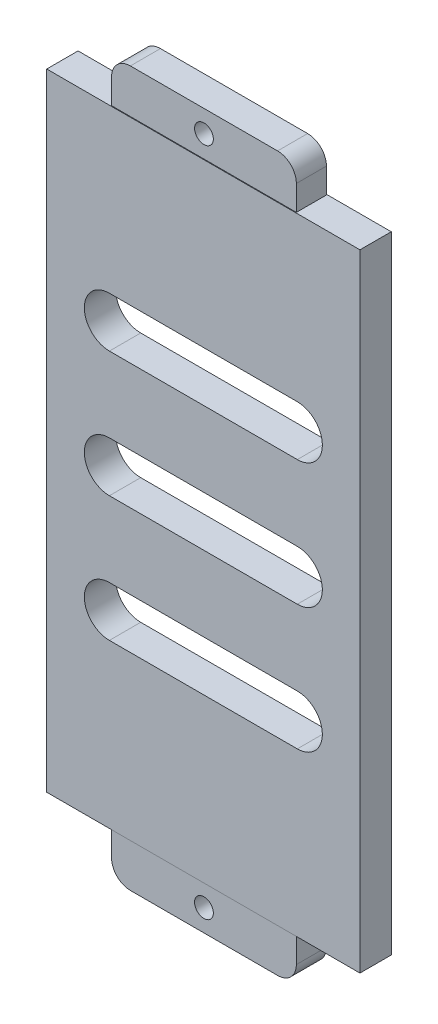
SolidWorks part; units mm, degrees
ref_plane "前视基准面" through (0, 0, 0) normal (0, 0, 1) x (1, 0, 0)
ref_plane "上视基准面" through (0, 0, 0) normal (0, 1, 0) x (1, 0, 0)
ref_plane "右视基准面" through (0, 0, 0) normal (1, 0, 0) x (0, 0, -1)
other "Configuration Table"
sketch "草图1" plane through (0, 0, 0) normal (0, 0, 1) x (1, 0, 0)
  line L1 (-25, 50) -> (25, 50)
  line L2 (-25, 50) -> (-25, -50)
  line L3 (-25, -50) -> (25, -50)
  line L4 (25, 50) -> (25, -50)
  line L5 (-25, 50) -> (25, -50) construction
  line L6 (-25, -50) -> (25, 50) construction
  point P0 (0, 0)
  dimension "D1" = 50
  dimension "D2" = 100
extrude "凸台-拉伸1" add sketch "草图1" against normal blind 5
sketch "草图2" plane through (0, 50, 0) normal (0, 1, 0) x (1, 0, 0)
  line L0 (-25, 2.5) -> (25, 2.5)
  line L1 (-25, 5) -> (-25, 0) construction
  line L2 (25, 5) -> (25, 0) construction
  line L4 (-14.75, 4.9) -> (14.75, 4.9)
  line L5 (-14.75, 4.9) -> (-14.75, 0.1)
  line L6 (-14.75, 0.1) -> (14.75, 0.1)
  line L7 (14.75, 4.9) -> (14.75, 0.1)
  line L8 (-14.75, 4.9) -> (14.75, 0.1) construction
  line L9 (-14.75, 0.1) -> (14.75, 4.9) construction
  point P6 (0, 2.5)
  dimension "D1" = 29.5
  dimension "D2" = 4.8
extrude "凸台-拉伸2" add sketch "草图2" along normal blind 7 contours L7 L4 L5 L0 | L7 L0 L5 L6
sketch "草图3" plane through (0, -50, 0) normal (0, -1, 0) x (1, 0, 0)
  line L0 (-25, -2.5) -> (25, -2.5)
  line L1 (-25, -5) -> (-25, 0) construction
  line L2 (25, -5) -> (25, 0) construction
  line L4 (-14.75, -0.1) -> (14.75, -0.1)
  line L5 (-14.75, -0.1) -> (-14.75, -4.9)
  line L6 (-14.75, -4.9) -> (14.75, -4.9)
  line L7 (14.75, -0.1) -> (14.75, -4.9)
  line L8 (-14.75, -0.1) -> (14.75, -4.9) construction
  line L9 (-14.75, -4.9) -> (14.75, -0.1) construction
  point P6 (0, -2.5)
  dimension "D1" = 29.5
  dimension "D2" = 4.8
extrude "凸台-拉伸3" add sketch "草图3" along normal blind 7 contours L7 L4 L5 L0 | L7 L0 L5 L6
sketch "草图4" plane through (0, 0, 0) normal (0, 0, 1) x (1, 0, 0)
  line L0 (0, 34.6167) -> (0, -35.3373)
  line L1 (-25, 20) -> (25, 20)
  line L2 (-25, 50) -> (-25, -50) construction
  line L3 (25, -50) -> (25, 50) construction
  line L4 (-25, 0) -> (25, 0)
  line L5 (-25, -20) -> (25, -20)
  line L6 (-15, 20) -> (15, 20) construction
  line L7 (-15, 24) -> (15, 24)
  line L8 (-15, 16) -> (15, 16)
  line L9 (-15, 0) -> (15, 0) construction
  line L10 (-15, 4) -> (15, 4)
  line L11 (-15, -4) -> (15, -4)
  line L12 (-15, -20) -> (15, -20) construction
  line L13 (-15, -16) -> (15, -16)
  line L14 (-15, -24) -> (15, -24)
  arc A0 (-15, 24) -> (-15, 16) centre (-15, 20) ccw
  arc A1 (15, 16) -> (15, 24) centre (15, 20) ccw
  arc A2 (-15, 4) -> (-15, -4) centre (-15, 0) ccw
  arc A3 (15, -4) -> (15, 4) centre (15, 0) ccw
  arc A4 (-15, -16) -> (-15, -24) centre (-15, -20) ccw
  arc A5 (15, -24) -> (15, -16) centre (15, -20) ccw
  point P13 (0, 20)
  point P14 (0, 0)
  point P15 (0, -20)
  point P18 (0, 20)
  point P24 (0, 0)
  point P31 (0, -20)
  dimension "D6" = 4
  dimension "D7" = 4
  dimension "D8" = 4
  dimension "D1" = 20
  dimension "D2" = 20
  dimension "D3" = 30
  dimension "D4" = 30
  dimension "D5" = 30
extrude "切除-拉伸1" cut sketch "草图4" against normal blind 5 contours L7 A0 L1 L0 | L1 A1 L7 L0 | L1 A0 L8 L0 | L8 A1 L1 L0 | L10 A2 L4 L0 | L4 A3 L10 L0 | L4 A2 L11 L0 | L11 A3 L4 L0 | L13 A4 L5 L0 | L5 A4 L14 L0 | L5 A5 L13 L0 | L14 A5 L5 L0
fillet "圆角1" radius 3 4 edges at (14.75, 57, -2.5) (-14.75, 57, -2.5) (-14.75, -57, -2.5) (14.75, -57, -2.5)
sketch "草图5" plane through (0, 0, -0.1) normal (0, 0, 1) x (1, 0, 0)
  line L0 (-14.75, 53.5) -> (14.75, 53.5) construction
  line L3 (0, 57) -> (0, 50) construction
  line L4 (-11.75, 57) -> (11.75, 57) construction
  line L5 (-14.75, 50) -> (14.75, 50) construction
  line L8 (-14.75, 54) -> (-14.75, 50) construction
  line L9 (14.75, 54) -> (14.75, 50) construction
  circle A0 centre (0, 53.5) radius 1.5
  point P12 (0, 53.5)
  dimension "D2" = 3
  dimension "D1" = 3.5
extrude "切除-拉伸2" cut sketch "草图5" against normal through all
sketch "草图6" plane through (0, 0, -0.1) normal (0, 0, 1) x (1, 0, 0)
  line L0 (0, -50) -> (0, -57) construction
  line L1 (-14.75, -50) -> (14.75, -50) construction
  line L2 (-11.75, -57) -> (11.75, -57) construction
  line L3 (-14.75, -53.5) -> (14.75, -53.5) construction
  line L4 (-14.75, -54) -> (-14.75, -50) construction
  line L5 (14.75, -54) -> (14.75, -50) construction
  circle A0 centre (0, -53.5) radius 1.5
  point P12 (0, -53.5)
  dimension "D2" = 3
  dimension "D1" = 3.5
extrude "切除-拉伸3" cut sketch "草图6" against normal through all
